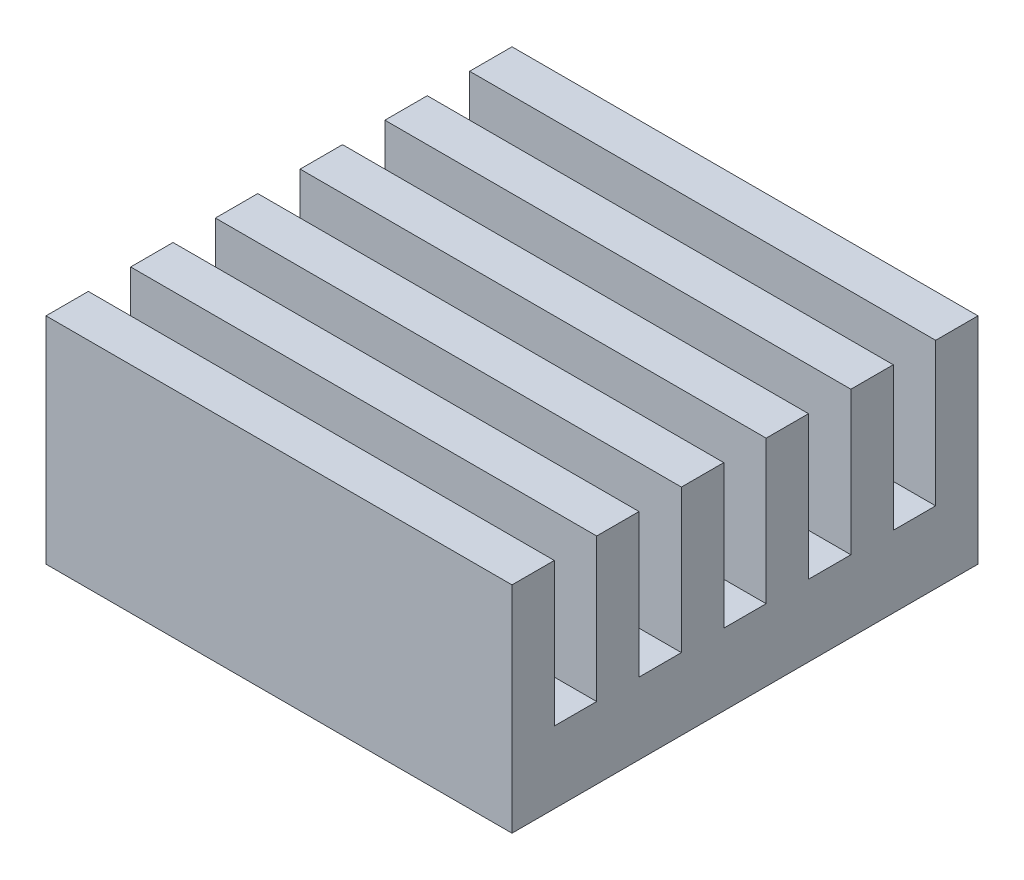
SolidWorks part; units mm, degrees
ref_plane "前视基准面" through (0, 0, 0) normal (0, 0, 1) x (1, 0, 0)
ref_plane "上视基准面" through (0, 0, 0) normal (0, 1, 0) x (1, 0, 0)
ref_plane "右视基准面" through (0, 0, 0) normal (1, 0, 0) x (0, 0, -1)
sketch "Sketch1" plane through (0, 0, 0) normal (0, 1, 0) x (1, 0, 0)
  line L1 (-32.5, -32.5) -> (32.5, -32.5)
  line L2 (-32.5, -32.5) -> (-32.5, 32.5)
  line L3 (-32.5, 32.5) -> (32.5, 32.5)
  line L4 (32.5, -32.5) -> (32.5, 32.5)
  line L5 (-32.5, -32.5) -> (32.5, 32.5) construction
  line L6 (-32.5, 32.5) -> (32.5, -32.5) construction
  point P0 (0, 0)
  dimension "D1" = 65
  dimension "D2" = 65
extrude "Extrude1" add sketch "Sketch1" along normal blind 30
sketch "Sketch2" plane through (0, 30, 0) normal (0, 1, 0) x (1, 0, 0)
  line L0 (-32.5, 32.5) -> (-32.5, -32.5) construction
  line L1 (-32.5, 26.59) -> (32.5, 26.59)
  line L2 (-32.5, 26.59) -> (-32.5, 20.68)
  line L3 (-32.5, 20.68) -> (32.5, 20.68)
  line L4 (32.5, 26.59) -> (32.5, 20.68)
  line L5 (32.5, -32.5) -> (32.5, 32.5) construction
  line L6 (32.5, 32.5) -> (-32.5, 32.5) construction
  line L7 (-32.5, 14.77) -> (-32.5, 8.86)
  line L8 (-32.5, 14.77) -> (32.5, 14.77)
  line L9 (32.5, 14.77) -> (32.5, 8.86)
  line L10 (-32.5, 8.86) -> (32.5, 8.86)
  line L11 (-32.5, 2.95) -> (-32.5, -2.96)
  line L12 (-32.5, 2.95) -> (32.5, 2.95)
  line L13 (32.5, 2.95) -> (32.5, -2.96)
  line L14 (-32.5, -2.96) -> (32.5, -2.96)
  line L15 (-32.5, -8.87) -> (-32.5, -14.78)
  line L16 (-32.5, -8.87) -> (32.5, -8.87)
  line L17 (32.5, -8.87) -> (32.5, -14.78)
  line L18 (-32.5, -14.78) -> (32.5, -14.78)
  line L19 (-32.5, -20.69) -> (-32.5, -26.6)
  line L20 (-32.5, -20.69) -> (32.5, -20.69)
  line L21 (32.5, -20.69) -> (32.5, -26.6)
  line L22 (-32.5, -26.6) -> (32.5, -26.6)
  dimension "D1" = 5.91
  dimension "D2" = 5.91
  dimension "D3" = 5
extrude "Extrude2" cut sketch "Sketch2" against normal blind 20
sketch "Sketch3" plane through (0, 0, 0) normal (0, -1, 0) x (1, 0, 0)
  line L1 (-25, 25) -> (25, 25)
  line L2 (-25, 25) -> (-25, -25)
  line L3 (-25, -25) -> (25, -25)
  line L4 (25, 25) -> (25, -25)
  line L5 (-25, 25) -> (25, -25) construction
  line L6 (-25, -25) -> (25, 25) construction
  point P0 (0, 0)
  dimension "D1" = 50
  dimension "D2" = 50
extrude "Extrude3" add sketch "Sketch3" along normal blind 1
